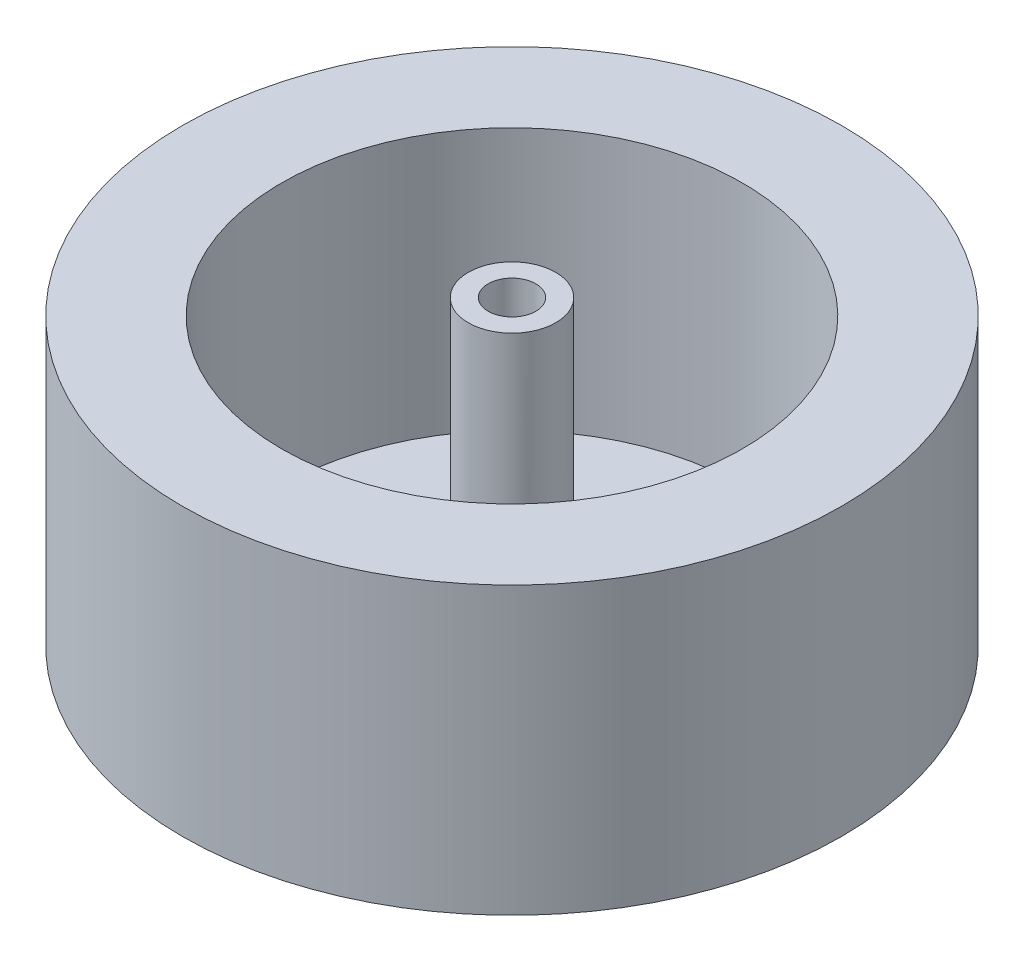
SolidWorks part; units mm, degrees
ref_plane "前视基准面" through (0, 0, 0) normal (0, 0, 1) x (1, 0, 0)
ref_plane "上视基准面" through (0, 0, 0) normal (0, 1, 0) x (1, 0, 0)
ref_plane "右视基准面" through (0, 0, 0) normal (1, 0, 0) x (0, 0, -1)
sketch "草图1" plane through (0, 0, 0) normal (0, 1, 0) x (1, 0, 0)
  circle A0 centre (0, 0) radius 41.5
  circle A1 centre (0, 0) radius 29
  dimension "D1" = 58
  dimension "D2" = 83
extrude "凸台-拉伸1" add sketch "草图1" along normal blind 33
sketch "草图2" plane through (0, 0, 0) normal (0, -1, 0) x (1, 0, 0)
  circle A0 centre (0, 0) radius 41.5
  dimension "D1" = 83
extrude "凸台-拉伸2" add sketch "草图2" along normal blind 3
sketch "草图3" plane through (0, 0, 0) normal (0, 1, 0) x (1, 0, 0)
  circle A0 centre (0, 0) radius 2
extrude "切除-拉伸1" cut sketch "草图3" against normal through all
sketch "草图4" plane through (0, 0, 0) normal (0, 1, 0) x (1, 0, 0)
  circle A0 centre (0, 0) radius 5.5
  circle A1 centre (0, 0) radius 3
extrude "凸台-拉伸3" add sketch "草图4" along normal blind 35
